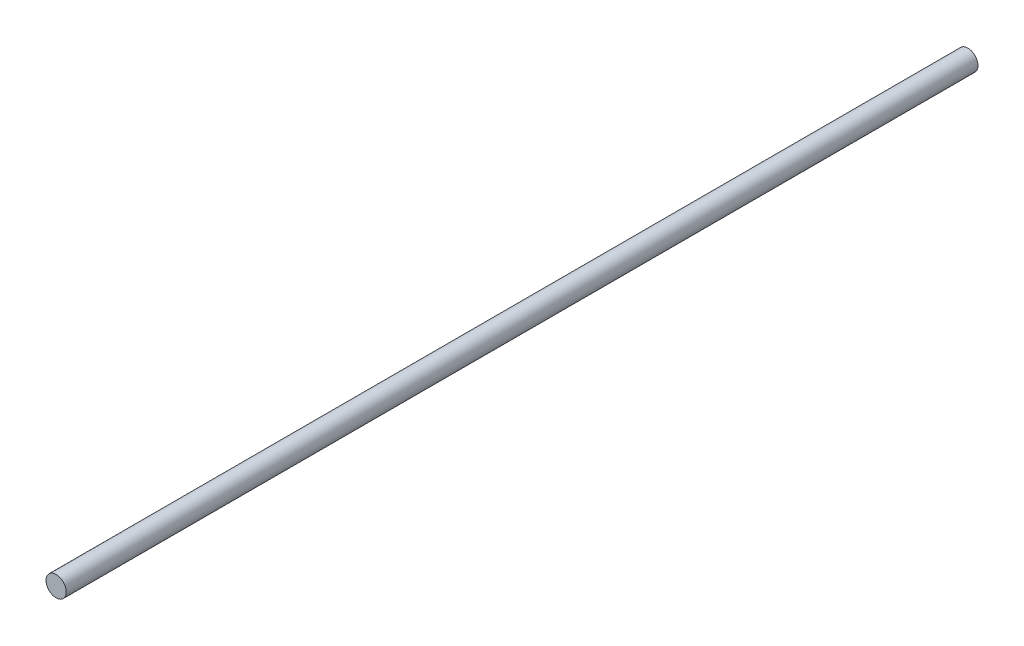
SolidWorks part; units mm, degrees
material "AISI 304"
ref_plane "Plano frontal" through (0, 0, 0) normal (0, 0, 1) x (1, 0, 0)
ref_plane "Plano superior" through (0, 0, 0) normal (0, 1, 0) x (1, 0, 0)
ref_plane "Plano direito" through (0, 0, 0) normal (1, 0, 0) x (0, 0, -1)
sketch "Esboço1" plane through (0, 0, 0) normal (0, 0, 1) x (1, 0, 0)
  circle A0 centre (0, 0) radius 4
  dimension "D1" = 8
extrude "Ressalto-extrusão1" add sketch "Esboço1" along normal blind 360
